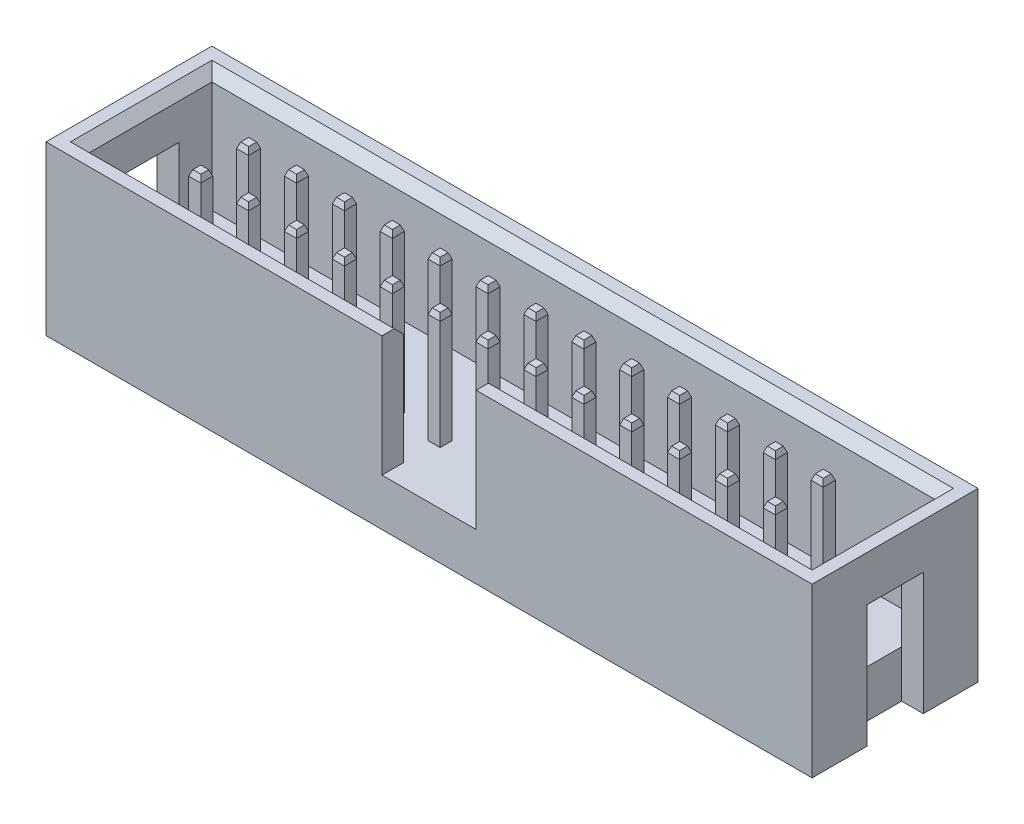
SolidWorks part; units mm, degrees
ref_plane "Front Plane" through (0, 0, 0) normal (0, 0, 1) x (1, 0, 0)
ref_plane "Top Plane" through (0, 0, 0) normal (0, 1, 0) x (1, 0, 0)
ref_plane "Right Plane" through (0, 0, 0) normal (1, 0, 0) x (0, 0, -1)
sketch "Sketch1" plane through (0, 0, 0) normal (0, 1, 0) x (1, 0, 0)
  line L1 (-20.32, 4.4) -> (20.32, 4.4)
  line L2 (-20.32, 4.4) -> (-20.32, -4.4)
  line L3 (-20.32, -4.4) -> (20.32, -4.4)
  line L4 (20.32, 4.4) -> (20.32, -4.4)
  line L5 (-20.32, 4.4) -> (20.32, -4.4) construction
  line L6 (-20.32, -4.4) -> (20.32, 4.4) construction
  point P0 (0, 0)
  dimension "D1" = 40.64
  dimension "D2" = 8.8
extrude "Boss-Extrude1" add sketch "Sketch1" along normal blind 2.5
sketch "Sketch2" plane through (0, 2.5, 0) normal (0, 1, 0) x (1, 0, 0)
  line L0 (0, -1000) -> (0, 49000) construction
  line L1 (20.32, 4.4) -> (-20.32, 4.4)
  line L2 (20.32, 4.4) -> (-20.32, 4.4) construction
  line L3 (-20.32, 4.4) -> (-20.32, -4.4)
  line L4 (-20.32, -4.4) -> (-2.5, -4.4)
  line L5 (-20.32, -4.4) -> (20.32, -4.4) construction
  line L6 (-2.5, -4.4) -> (-2.5, -3.25)
  line L7 (-2.5, -3.25) -> (-19.17, -3.25)
  line L8 (-19.17, -3.25) -> (-19.17, 3.25)
  line L9 (-19.17, 3.25) -> (19.17, 3.25)
  line L10 (19.17, 0) -> (20.32, 0) construction
  line L11 (-19.17, 0) -> (-20.32, 0) construction
  line L12 (19.17, -3.25) -> (19.17, 3.25)
  line L13 (2.5, -3.25) -> (19.17, -3.25)
  line L14 (2.5, -4.4) -> (2.5, -3.25)
  line L15 (20.32, -4.4) -> (2.5, -4.4)
  line L16 (20.32, 4.4) -> (20.32, -4.4)
  point P22 (0, 3.25)
  point P27 (0, 4.4)
  dimension "D1" = 6.5
  dimension "D2" = 19.17
  dimension "D3" = 2.5
extrude "Boss-Extrude2" add sketch "Sketch2" along normal blind 6.4
sketch "Sketch3" plane through (0, 0, 0) normal (0, -1, 0) x (1, 0, 0)
  line L0 (20.32, 4.4) -> (20.32, -4.4) construction
  line L1 (20.32, -1.5) -> (19.17, -1.5)
  line L2 (20.32, -1.5) -> (20.32, 1.5)
  line L3 (20.32, 1.5) -> (19.17, 1.5)
  line L4 (19.17, -1.5) -> (19.17, 1.5)
  line L5 (19.17, 0) -> (20.32, 0) construction
  line L6 (0, 4.4) -> (0, -4.4) construction
  line L7 (-20.32, 4.4) -> (20.32, 4.4) construction
  line L8 (20.32, -4.4) -> (-20.32, -4.4) construction
  line L9 (-19.17, 0) -> (-20.32, 0) construction
  line L10 (-19.17, -1.5) -> (-19.17, 1.5)
  line L11 (-20.32, 1.5) -> (-19.17, 1.5)
  line L12 (-20.32, -1.5) -> (-20.32, 1.5)
  line L13 (-20.32, -1.5) -> (-19.17, -1.5)
  dimension "D1" = 1.15
  dimension "D2" = 3
extrude "Cut-Extrude1" cut sketch "Sketch3" against normal blind 6.5
sketch "Sketch4" plane through (0, 2.5, 0) normal (0, 1, 0) x (1, 0, 0)
  line L0 (-19.17, 0) -> (19.17, 0) construction
  line L1 (-15.56, 1.59) -> (-14.92, 1.59)
  line L2 (-15.56, 1.59) -> (-15.56, 0.95)
  line L3 (-15.56, 0.95) -> (-14.92, 0.95)
  line L4 (-14.92, 1.59) -> (-14.92, 0.95)
  line L5 (-15.56, 1.59) -> (-14.92, 0.95) construction
  line L6 (-15.56, 0.95) -> (-14.92, 1.59) construction
  line L7 (-19.17, -1.5) -> (-19.17, 1.5) construction
  line L8 (19.17, 3.25) -> (19.17, -3.25) construction
  line L9 (-20.32, 4.4) -> (-20.32, -4.4) construction
  line L10 (-13.02, 1.59) -> (-12.38, 1.59)
  line L11 (-13.02, 1.59) -> (-13.02, 0.95)
  line L12 (-13.02, 0.95) -> (-12.38, 0.95)
  line L13 (-12.38, 1.59) -> (-12.38, 0.95)
  line L14 (-13.02, 1.59) -> (-12.38, 0.95) construction
  line L15 (-13.02, 0.95) -> (-12.38, 1.59) construction
  line L16 (-10.48, 1.59) -> (-9.84, 1.59)
  line L17 (-10.48, 1.59) -> (-10.48, 0.95)
  line L18 (-10.48, 0.95) -> (-9.84, 0.95)
  line L19 (-9.84, 1.59) -> (-9.84, 0.95)
  line L20 (-10.48, 1.59) -> (-9.84, 0.95) construction
  line L21 (-10.48, 0.95) -> (-9.84, 1.59) construction
  line L22 (-7.94, 1.59) -> (-7.3, 1.59)
  line L23 (-7.94, 1.59) -> (-7.94, 0.95)
  line L24 (-7.94, 0.95) -> (-7.3, 0.95)
  line L25 (-7.3, 1.59) -> (-7.3, 0.95)
  line L26 (-7.94, 1.59) -> (-7.3, 0.95) construction
  line L27 (-7.94, 0.95) -> (-7.3, 1.59) construction
  line L28 (-5.4, 1.59) -> (-4.76, 1.59)
  line L29 (-5.4, 1.59) -> (-5.4, 0.95)
  line L30 (-5.4, 0.95) -> (-4.76, 0.95)
  line L31 (-4.76, 1.59) -> (-4.76, 0.95)
  line L32 (-5.4, 1.59) -> (-4.76, 0.95) construction
  line L33 (-5.4, 0.95) -> (-4.76, 1.59) construction
  line L34 (-2.86, 1.59) -> (-2.22, 1.59)
  line L35 (-2.86, 1.59) -> (-2.86, 0.95)
  line L36 (-2.86, 0.95) -> (-2.22, 0.95)
  line L37 (-2.22, 1.59) -> (-2.22, 0.95)
  line L38 (-2.86, 1.59) -> (-2.22, 0.95) construction
  line L39 (-2.86, 0.95) -> (-2.22, 1.59) construction
  line L40 (-0.32, 1.59) -> (0.32, 1.59)
  line L41 (-0.32, 1.59) -> (-0.32, 0.95)
  line L42 (-0.32, 0.95) -> (0.32, 0.95)
  line L43 (0.32, 1.59) -> (0.32, 0.95)
  line L44 (-0.32, 1.59) -> (0.32, 0.95) construction
  line L45 (-0.32, 0.95) -> (0.32, 1.59) construction
  line L46 (2.22, 1.59) -> (2.86, 1.59)
  line L47 (2.22, 1.59) -> (2.22, 0.95)
  line L48 (2.22, 0.95) -> (2.86, 0.95)
  line L49 (2.86, 1.59) -> (2.86, 0.95)
  line L50 (2.22, 1.59) -> (2.86, 0.95) construction
  line L51 (2.22, 0.95) -> (2.86, 1.59) construction
  line L52 (4.76, 1.59) -> (5.4, 1.59)
  line L53 (4.76, 1.59) -> (4.76, 0.95)
  line L54 (4.76, 0.95) -> (5.4, 0.95)
  line L55 (5.4, 1.59) -> (5.4, 0.95)
  line L56 (4.76, 1.59) -> (5.4, 0.95) construction
  line L57 (4.76, 0.95) -> (5.4, 1.59) construction
  line L58 (7.3, 1.59) -> (7.94, 1.59)
  line L59 (7.3, 1.59) -> (7.3, 0.95)
  line L60 (7.3, 0.95) -> (7.94, 0.95)
  line L61 (7.94, 1.59) -> (7.94, 0.95)
  line L62 (7.3, 1.59) -> (7.94, 0.95) construction
  line L63 (7.3, 0.95) -> (7.94, 1.59) construction
  line L64 (9.84, 1.59) -> (10.48, 1.59)
  line L65 (9.84, 1.59) -> (9.84, 0.95)
  line L66 (9.84, 0.95) -> (10.48, 0.95)
  line L67 (10.48, 1.59) -> (10.48, 0.95)
  line L68 (9.84, 1.59) -> (10.48, 0.95) construction
  line L69 (9.84, 0.95) -> (10.48, 1.59) construction
  line L70 (12.38, 1.59) -> (13.02, 1.59)
  line L71 (12.38, 1.59) -> (12.38, 0.95)
  line L72 (12.38, 0.95) -> (13.02, 0.95)
  line L73 (13.02, 1.59) -> (13.02, 0.95)
  line L74 (12.38, 1.59) -> (13.02, 0.95) construction
  line L75 (12.38, 0.95) -> (13.02, 1.59) construction
  line L76 (14.92, 1.59) -> (15.56, 1.59)
  line L77 (14.92, 1.59) -> (14.92, 0.95)
  line L78 (14.92, 0.95) -> (15.56, 0.95)
  line L79 (15.56, 1.59) -> (15.56, 0.95)
  line L80 (14.92, 1.59) -> (15.56, 0.95) construction
  line L81 (14.92, 0.95) -> (15.56, 1.59) construction
  line L82 (-13.02, -0.95) -> (-12.38, -0.95)
  line L83 (-13.02, -0.95) -> (-13.02, -1.59)
  line L84 (-13.02, -1.59) -> (-12.38, -1.59)
  line L85 (-12.38, -0.95) -> (-12.38, -1.59)
  line L86 (-13.02, -0.95) -> (-12.38, -1.59) construction
  line L87 (-13.02, -1.59) -> (-12.38, -0.95) construction
  line L88 (-10.48, -0.95) -> (-9.84, -0.95)
  line L89 (-10.48, -0.95) -> (-10.48, -1.59)
  line L90 (-10.48, -1.59) -> (-9.84, -1.59)
  line L91 (-9.84, -0.95) -> (-9.84, -1.59)
  line L92 (-10.48, -0.95) -> (-9.84, -1.59) construction
  line L93 (-10.48, -1.59) -> (-9.84, -0.95) construction
  line L94 (-7.94, -0.95) -> (-7.3, -0.95)
  line L95 (-7.94, -0.95) -> (-7.94, -1.59)
  line L96 (-7.94, -1.59) -> (-7.3, -1.59)
  line L97 (-7.3, -0.95) -> (-7.3, -1.59)
  line L98 (-7.94, -0.95) -> (-7.3, -1.59) construction
  line L99 (-7.94, -1.59) -> (-7.3, -0.95) construction
  line L100 (-5.4, -0.95) -> (-4.76, -0.95)
  line L101 (-5.4, -0.95) -> (-5.4, -1.59)
  line L102 (-5.4, -1.59) -> (-4.76, -1.59)
  line L103 (-4.76, -0.95) -> (-4.76, -1.59)
  line L104 (-5.4, -0.95) -> (-4.76, -1.59) construction
  line L105 (-5.4, -1.59) -> (-4.76, -0.95) construction
  line L106 (-2.86, -0.95) -> (-2.22, -0.95)
  line L107 (-2.86, -0.95) -> (-2.86, -1.59)
  line L108 (-2.86, -1.59) -> (-2.22, -1.59)
  line L109 (-2.22, -0.95) -> (-2.22, -1.59)
  line L110 (-2.86, -0.95) -> (-2.22, -1.59) construction
  line L111 (-2.86, -1.59) -> (-2.22, -0.95) construction
  line L112 (-0.32, -0.95) -> (0.32, -0.95)
  line L113 (-0.32, -0.95) -> (-0.32, -1.59)
  line L114 (-0.32, -1.59) -> (0.32, -1.59)
  line L115 (0.32, -0.95) -> (0.32, -1.59)
  line L116 (-0.32, -0.95) -> (0.32, -1.59) construction
  line L117 (-0.32, -1.59) -> (0.32, -0.95) construction
  line L118 (2.22, -0.95) -> (2.86, -0.95)
  line L119 (2.22, -0.95) -> (2.22, -1.59)
  line L120 (2.22, -1.59) -> (2.86, -1.59)
  line L121 (2.86, -0.95) -> (2.86, -1.59)
  line L122 (2.22, -0.95) -> (2.86, -1.59) construction
  line L123 (2.22, -1.59) -> (2.86, -0.95) construction
  line L124 (4.76, -0.95) -> (5.4, -0.95)
  line L125 (4.76, -0.95) -> (4.76, -1.59)
  line L126 (4.76, -1.59) -> (5.4, -1.59)
  line L127 (5.4, -0.95) -> (5.4, -1.59)
  line L128 (4.76, -0.95) -> (5.4, -1.59) construction
  line L129 (4.76, -1.59) -> (5.4, -0.95) construction
  line L130 (7.3, -0.95) -> (7.94, -0.95)
  line L131 (7.3, -0.95) -> (7.3, -1.59)
  line L132 (7.3, -1.59) -> (7.94, -1.59)
  line L133 (7.94, -0.95) -> (7.94, -1.59)
  line L134 (7.3, -0.95) -> (7.94, -1.59) construction
  line L135 (7.3, -1.59) -> (7.94, -0.95) construction
  line L136 (9.84, -0.95) -> (10.48, -0.95)
  line L137 (9.84, -0.95) -> (9.84, -1.59)
  line L138 (9.84, -1.59) -> (10.48, -1.59)
  line L139 (10.48, -0.95) -> (10.48, -1.59)
  line L140 (9.84, -0.95) -> (10.48, -1.59) construction
  line L141 (9.84, -1.59) -> (10.48, -0.95) construction
  line L142 (12.38, -0.95) -> (13.02, -0.95)
  line L143 (12.38, -0.95) -> (12.38, -1.59)
  line L144 (12.38, -1.59) -> (13.02, -1.59)
  line L145 (13.02, -0.95) -> (13.02, -1.59)
  line L146 (12.38, -0.95) -> (13.02, -1.59) construction
  line L147 (12.38, -1.59) -> (13.02, -0.95) construction
  line L148 (14.92, -0.95) -> (15.56, -0.95)
  line L149 (14.92, -0.95) -> (14.92, -1.59)
  line L150 (14.92, -1.59) -> (15.56, -1.59)
  line L151 (15.56, -0.95) -> (15.56, -1.59)
  line L152 (14.92, -0.95) -> (15.56, -1.59) construction
  line L153 (14.92, -1.59) -> (15.56, -0.95) construction
  line L154 (-15.56, -0.95) -> (-14.92, -0.95)
  line L155 (-15.56, -0.95) -> (-15.56, -1.59)
  line L156 (-15.56, -1.59) -> (-14.92, -1.59)
  line L157 (-14.92, -0.95) -> (-14.92, -1.59)
  line L158 (-15.56, -0.95) -> (-14.92, -1.59) construction
  line L159 (-15.56, -1.59) -> (-14.92, -0.95) construction
  point P0 (-15.24, 1.27)
  point P16 (-12.7, 1.27)
  point P21 (-10.16, 1.27)
  point P26 (-7.62, 1.27)
  point P31 (-5.08, 1.27)
  point P36 (-2.54, 1.27)
  point P41 (0, 1.27)
  point P46 (2.54, 1.27)
  point P51 (5.08, 1.27)
  point P56 (7.62, 1.27)
  point P61 (10.16, 1.27)
  point P66 (12.7, 1.27)
  point P71 (15.24, 1.27)
  point P76 (-12.7, -1.27)
  point P81 (-10.16, -1.27)
  point P86 (-7.62, -1.27)
  point P91 (-5.08, -1.27)
  point P96 (-2.54, -1.27)
  point P101 (0, -1.27)
  point P106 (2.54, -1.27)
  point P111 (5.08, -1.27)
  point P116 (7.62, -1.27)
  point P121 (10.16, -1.27)
  point P126 (12.7, -1.27)
  point P131 (15.24, -1.27)
  point P136 (-15.24, -1.27)
  dimension "D1" = 0.64
  dimension "D2" = 0.64
  dimension "D3" = 1.27
  dimension "D4" = 5.08
  dimension "D5" = 13
  dimension "D6" = 2
extrude "Boss-Extrude3" add sketch "Sketch4" along normal blind 6.1 and the other way blind 5.5
chamfer "Chamfer2" distance 0.2 angle 70 104 edges at (-14.92, -3, 1.27) (-15.24, -3, 0.95) (-15.56, -3, 1.27) (-15.24, -3, 1.59) (15.56, -3, 1.27) (15.24, -3, 0.95) (14.92, -3, 1.27) (15.24, -3, 1.59) (13.02, -3, 1.27) (12.7, -3, 0.95) (12.38, -3, 1.27) (12.7, -3, 1.59) (10.48, -3, 1.27) (10.16, -3, 0.95) (9.84, -3, 1.27) (10.16, -3, 1.59) (7.94, -3, 1.27) (7.62, -3, 0.95) (7.3, -3, 1.27) (7.62, -3, 1.59) (5.4, -3, 1.27) (5.08, -3, 0.95) (4.76, -3, 1.27) (5.08, -3, 1.59) (2.86, -3, 1.27) (2.54, -3, 0.95) (2.22, -3, 1.27) (2.54, -3, 1.59) (0.32, -3, 1.27) (0, -3, 0.95) (-0.32, -3, 1.27) (0, -3, 1.59) (-2.22, -3, 1.27) (-2.54, -3, 0.95) (-2.86, -3, 1.27) (-2.54, -3, 1.59) (-4.76, -3, 1.27) (-5.08, -3, 0.95) (-5.4, -3, 1.27) (-5.08, -3, 1.59) (-7.3, -3, 1.27) (-7.62, -3, 0.95) (-7.94, -3, 1.27) (-7.62, -3, 1.59) (-9.84, -3, 1.27) (-10.16, -3, 0.95) (-10.48, -3, 1.27) (-10.16, -3, 1.59) (-12.38, -3, 1.27) (-12.7, -3, 0.95) (-13.02, -3, 1.27) (-12.7, -3, 1.59) (15.56, -3, -1.27) (15.24, -3, -1.59) (14.92, -3, -1.27) (15.24, -3, -0.95) (13.02, -3, -1.27) (12.7, -3, -1.59) (12.38, -3, -1.27) (12.7, -3, -0.95) (10.48, -3, -1.27) (10.16, -3, -1.59) (9.84, -3, -1.27) (10.16, -3, -0.95) (7.94, -3, -1.27) (7.62, -3, -1.59) (7.3, -3, -1.27) (7.62, -3, -0.95) (5.4, -3, -1.27) (5.08, -3, -1.59) (4.76, -3, -1.27) (5.08, -3, -0.95) (2.86, -3, -1.27) (2.54, -3, -1.59) (2.22, -3, -1.27) (2.54, -3, -0.95) (0.32, -3, -1.27) (0, -3, -1.59) (-0.32, -3, -1.27) (0, -3, -0.95) (-2.22, -3, -1.27) (-2.54, -3, -1.59) (-2.86, -3, -1.27) (-2.54, -3, -0.95) (-4.76, -3, -1.27) (-5.08, -3, -1.59) (-5.4, -3, -1.27) (-5.08, -3, -0.95) (-7.3, -3, -1.27) (-7.62, -3, -1.59) (-7.94, -3, -1.27) (-7.62, -3, -0.95) (-9.84, -3, -1.27) (-10.16, -3, -1.59) (-10.48, -3, -1.27) (-10.16, -3, -0.95) (-12.38, -3, -1.27) (-12.7, -3, -1.59) (-13.02, -3, -1.27) (-12.7, -3, -0.95) (-14.92, -3, -1.27) (-15.24, -3, -1.59) (-15.56, -3, -1.27) (-15.24, -3, -0.95)
chamfer "Chamfer3" distance 0.3 angle 20 104 edges at (-14.92, 8.6, 1.27) (-15.24, 8.6, 0.95) (-15.56, 8.6, 1.27) (-15.24, 8.6, 1.59) (15.56, 8.6, 1.27) (15.24, 8.6, 0.95) (14.92, 8.6, 1.27) (15.24, 8.6, 1.59) (13.02, 8.6, 1.27) (12.7, 8.6, 0.95) (12.38, 8.6, 1.27) (12.7, 8.6, 1.59) (10.48, 8.6, 1.27) (10.16, 8.6, 0.95) (9.84, 8.6, 1.27) (10.16, 8.6, 1.59) (7.94, 8.6, 1.27) (7.62, 8.6, 0.95) (7.3, 8.6, 1.27) (7.62, 8.6, 1.59) (5.4, 8.6, 1.27) (5.08, 8.6, 0.95) (4.76, 8.6, 1.27) (5.08, 8.6, 1.59) (2.86, 8.6, 1.27) (2.54, 8.6, 0.95) (2.22, 8.6, 1.27) (2.54, 8.6, 1.59) (0.32, 8.6, 1.27) (0, 8.6, 0.95) (-0.32, 8.6, 1.27) (0, 8.6, 1.59) (-2.22, 8.6, 1.27) (-2.54, 8.6, 0.95) (-2.86, 8.6, 1.27) (-2.54, 8.6, 1.59) (-4.76, 8.6, 1.27) (-5.08, 8.6, 0.95) (-5.4, 8.6, 1.27) (-5.08, 8.6, 1.59) (-7.3, 8.6, 1.27) (-7.62, 8.6, 0.95) (-7.94, 8.6, 1.27) (-7.62, 8.6, 1.59) (-9.84, 8.6, 1.27) (-10.16, 8.6, 0.95) (-10.48, 8.6, 1.27) (-10.16, 8.6, 1.59) (-12.38, 8.6, 1.27) (-12.7, 8.6, 0.95) (-13.02, 8.6, 1.27) (-12.7, 8.6, 1.59) (15.56, 8.6, -1.27) (15.24, 8.6, -1.59) (14.92, 8.6, -1.27) (15.24, 8.6, -0.95) (13.02, 8.6, -1.27) (12.7, 8.6, -1.59) (12.38, 8.6, -1.27) (12.7, 8.6, -0.95) (10.48, 8.6, -1.27) (10.16, 8.6, -1.59) (9.84, 8.6, -1.27) (10.16, 8.6, -0.95) (7.94, 8.6, -1.27) (7.62, 8.6, -1.59) (7.3, 8.6, -1.27) (7.62, 8.6, -0.95) (5.4, 8.6, -1.27) (5.08, 8.6, -1.59) (4.76, 8.6, -1.27) (5.08, 8.6, -0.95) (2.86, 8.6, -1.27) (2.54, 8.6, -1.59) (2.22, 8.6, -1.27) (2.54, 8.6, -0.95) (0.32, 8.6, -1.27) (0, 8.6, -1.59) (-0.32, 8.6, -1.27) (0, 8.6, -0.95) (-2.22, 8.6, -1.27) (-2.54, 8.6, -1.59) (-2.86, 8.6, -1.27) (-2.54, 8.6, -0.95) (-4.76, 8.6, -1.27) (-5.08, 8.6, -1.59) (-5.4, 8.6, -1.27) (-5.08, 8.6, -0.95) (-7.3, 8.6, -1.27) (-7.62, 8.6, -1.59) (-7.94, 8.6, -1.27) (-7.62, 8.6, -0.95) (-9.84, 8.6, -1.27) (-10.16, 8.6, -1.59) (-10.48, 8.6, -1.27) (-10.16, 8.6, -0.95) (-12.38, 8.6, -1.27) (-12.7, 8.6, -1.59) (-13.02, 8.6, -1.27) (-12.7, 8.6, -0.95) (-14.92, 8.6, -1.27) (-15.24, 8.6, -1.59) (-15.56, 8.6, -1.27) (-15.24, 8.6, -0.95)
chamfer "Chamfer4" distance 0.5 angle 45 5 edges at (10.835, 8.9, 3.25) (19.17, 8.9, 0) (-10.835, 8.9, 3.25) (-19.17, 8.9, 0) (0, 8.9, -3.25)
ref_point "Pin 1"
